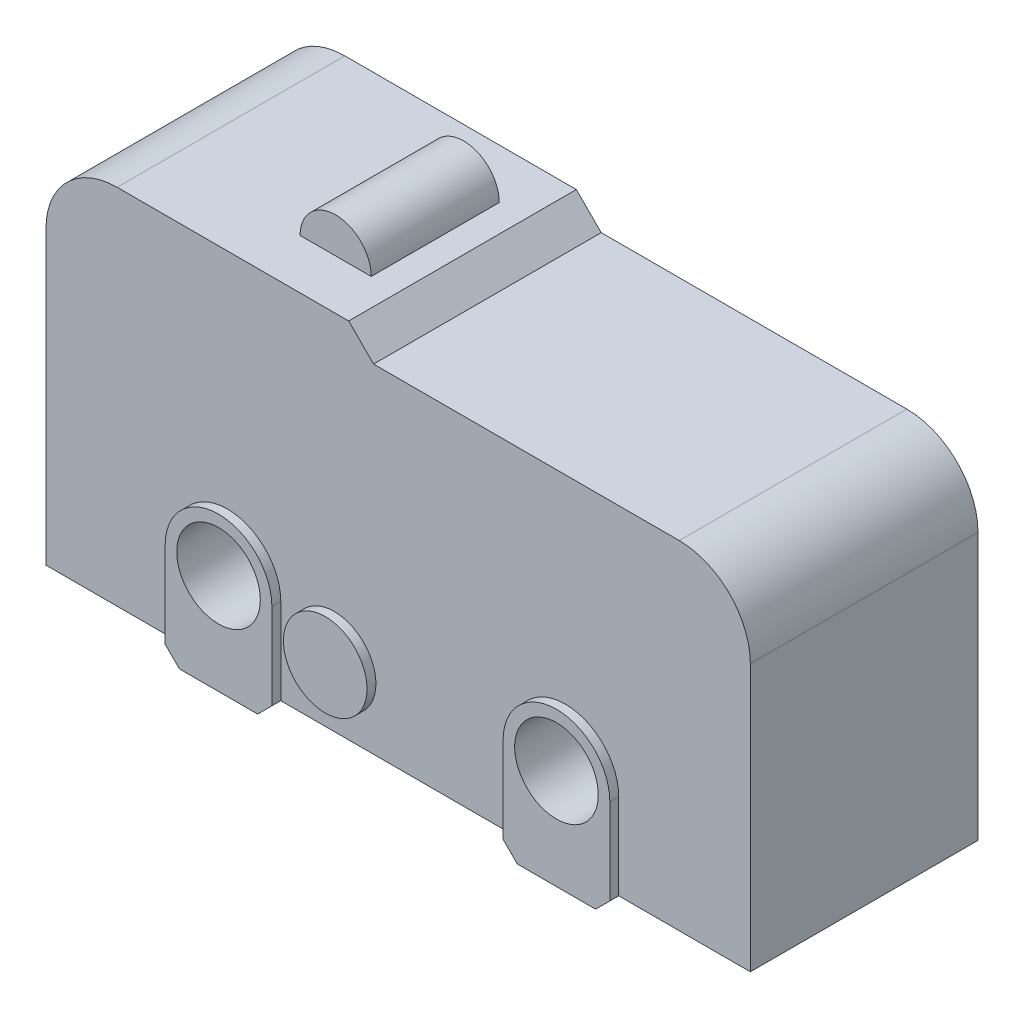
SolidWorks part; units mm, degrees
ref_plane "Front Plane" through (0, 0, 0) normal (0, 0, 1) x (1, 0, 0)
ref_plane "Top Plane" through (0, 0, 0) normal (0, 1, 0) x (1, 0, 0)
ref_plane "Right Plane" through (0, 0, 0) normal (1, 0, 0) x (0, 0, -1)
sketch "Sketch1" plane through (0, 0, 0) normal (0, 0, 1) x (1, 0, 0)
  line L0 (-6.3, 2.5) -> (-6.3, 0.0821)
  line L1 (-9.9, 0.0821) -> (-6.3, 0.0821)
  line L2 (-9.9, 0.0821) -> (-9.9, 8.2821)
  line L3 (-7.9, 10.2821) -> (-2.7324, 10.2821)
  line L4 (9.9, 0.0821) -> (9.9, 7.5821)
  line L5 (-5.9, -0.3179) -> (-6.3, 0.0821)
  line L6 (-3.3, 0.0821) -> (-3.3, 2.5)
  line L7 (-5.9, -0.3179) -> (-3.7, -0.3179)
  line L8 (3.2, 2.5) -> (3.2, 0.0821)
  line L9 (6.2, 2.5) -> (6.2, 0.0821)
  line L10 (-3.7, -0.3179) -> (-3.3, 0.0821)
  line L11 (3.2, 0.0821) -> (3.6, -0.3179)
  line L12 (3.6, -0.3179) -> (5.8, -0.3179)
  line L13 (5.8, -0.3179) -> (6.2, 0.0821)
  line L14 (-3.3, 0.0821) -> (3.2, 0.0821)
  line L15 (6.2, 0.0821) -> (9.9, 0.0821)
  line L16 (7.9, 9.5821) -> (-2.0324, 9.5821)
  line L17 (-2.7324, 10.2821) -> (-2.0324, 9.5821)
  circle A0 centre (-4.8, 2.5) radius 1.175
  circle A1 centre (4.7, 2.5) radius 1.175
  arc A2 (-3.3, 2.5) -> (-6.3, 2.5) centre (-4.8, 2.5) ccw
  arc A3 (6.2, 2.5) -> (3.2, 2.5) centre (4.7, 2.5) ccw
  circle A4 centre (-1.8, 1.8321) radius 1.175
  arc A5 (-9.9, 8.2821) -> (-7.9, 10.2821) centre (-7.9, 8.2821) cw
  arc A6 (7.9, 9.5821) -> (9.9, 7.5821) centre (7.9, 7.5821) cw
  arc A7 (-3.8, 10.2821) -> (-5.8, 10.2821) centre (-4.8, 10.2821) ccw
  point P25 (-9.9, 10.2821)
  dimension "D4" = 2.35
  dimension "D5" = 2.35
  dimension "D6" = 2.35
  dimension "D10" = 3
  dimension "D11" = 3
  dimension "D19" = 2
  dimension "D22" = 2
  dimension "D23" = 2
  dimension "D1" = 19.8
  dimension "D2" = 10.2
  dimension "D3" = 9.9
  dimension "D7" = 1.5
  dimension "D8" = 5.1
  dimension "D9" = 9.5
  dimension "D12" = 1.75
  dimension "D13" = 0.4
  dimension "D14" = 0.4
  dimension "D15" = 45
  dimension "D16" = 45
  dimension "D17" = 45
  dimension "D18" = 45
  dimension "D20" = 9.5
  dimension "D21" = 45
sketch "Sketch2" plane through (0, 0, 0) normal (0, 0, 1) x (1, 0, 0)
  line L0 (-7.9, 10.2821) -> (-2.7324, 10.2821) construction
  line L2 (7.9, 9.5821) -> (-2.0324, 9.5821) construction
  line L3 (9.9, 0.0821) -> (9.9, 7.5821) construction
  line L4 (6.2, 0.0821) -> (9.9, 0.0821) construction
  line L5 (5.8, -0.3179) -> (6.2, 0.0821) construction
  line L6 (3.6, -0.3179) -> (5.8, -0.3179) construction
  line L7 (3.2, 0.0821) -> (3.6, -0.3179) construction
  line L8 (-3.3, 0.0821) -> (3.2, 0.0821) construction
  line L9 (-3.7, -0.3179) -> (-3.3, 0.0821) construction
  line L10 (-5.9, -0.3179) -> (-3.7, -0.3179) construction
  line L11 (-5.9, -0.3179) -> (-6.3, 0.0821) construction
  line L12 (-9.9, 0.0821) -> (-6.3, 0.0821) construction
  line L13 (-9.9, 0.0821) -> (-9.9, 8.2821) construction
  line L14 (-7.9, 10.2821) -> (-1.3912, 10.2821)
  line L15 (-1.3912, 10.2821) -> (-0.6912, 9.5821)
  line L16 (7.9, 9.5821) -> (-0.6912, 9.5821)
  line L17 (9.9, 0.0821) -> (9.9, 7.5821)
  line L18 (6.2, 0.0821) -> (9.9, 0.0821)
  line L19 (5.8, -0.3179) -> (6.2, 0.0821)
  line L20 (3.6, -0.3179) -> (5.8, -0.3179)
  line L21 (3.2, 0.0821) -> (3.6, -0.3179)
  line L22 (-3.3, 0.0821) -> (3.2, 0.0821)
  line L23 (-3.7, -0.3179) -> (-3.3, 0.0821)
  line L24 (-5.9, -0.3179) -> (-3.7, -0.3179)
  line L25 (-5.9, -0.3179) -> (-6.3, 0.0821)
  line L26 (-9.9, 0.0821) -> (-6.3, 0.0821)
  line L27 (-9.9, 0.0821) -> (-9.9, 8.2821)
  arc A0 (-7.9, 10.2821) -> (-9.9, 8.2821) centre (-7.9, 8.2821) ccw construction
  arc A1 (9.9, 7.5821) -> (7.9, 9.5821) centre (7.9, 7.5821) ccw construction
  arc A2 (-7.9, 10.2821) -> (-9.9, 8.2821) centre (-7.9, 8.2821) ccw
  arc A3 (9.9, 7.5821) -> (7.9, 9.5821) centre (7.9, 7.5821) ccw
extrude "Boss-Extrude1" add sketch "Sketch2" along normal blind 6.4
sketch "Sketch4" plane through (0, 0, 6.4) normal (0, 0, 1) x (1, 0, 0)
  line L0 (-6.3, 2.5) -> (-6.3, 0.0821) construction
  line L1 (-3.3, 0.0821) -> (-3.3, 2.5) construction
  line L2 (-3.7, -0.3179) -> (-3.3, 0.0821) construction
  line L3 (-5.9, -0.3179) -> (-3.7, -0.3179) construction
  line L4 (-5.9, -0.3179) -> (-6.3, 0.0821) construction
  line L5 (3.2, 2.5) -> (3.2, 0.0821) construction
  line L6 (6.2, 2.5) -> (6.2, 0.0821) construction
  line L7 (5.8, -0.3179) -> (6.2, 0.0821) construction
  line L8 (3.6, -0.3179) -> (5.8, -0.3179) construction
  line L9 (3.2, 0.0821) -> (3.6, -0.3179) construction
  line L10 (-6.3, 2.5) -> (-6.3, 0.0821)
  line L11 (-3.3, 0.0821) -> (-3.3, 2.5)
  line L12 (-3.7, -0.3179) -> (-3.3, 0.0821)
  line L13 (-5.9, -0.3179) -> (-3.7, -0.3179)
  line L14 (-5.9, -0.3179) -> (-6.3, 0.0821)
  line L15 (3.2, 2.5) -> (3.2, 0.0821)
  line L16 (6.2, 2.5) -> (6.2, 0.0821)
  line L17 (5.8, -0.3179) -> (6.2, 0.0821)
  line L18 (3.6, -0.3179) -> (5.8, -0.3179)
  line L19 (3.2, 0.0821) -> (3.6, -0.3179)
  arc A0 (-3.3, 2.5) -> (-6.3, 2.5) centre (-4.8, 2.5) ccw construction
  arc A1 (6.2, 2.5) -> (3.2, 2.5) centre (4.7, 2.5) ccw construction
  circle A2 centre (-1.8, 1.8321) radius 1.175 construction
  arc A3 (-3.3, 2.5) -> (-6.3, 2.5) centre (-4.8, 2.5) ccw
  arc A4 (6.2, 2.5) -> (3.2, 2.5) centre (4.7, 2.5) ccw
  circle A5 centre (-1.8, 1.8321) radius 1.175
extrude "Boss-Extrude2" add sketch "Sketch4" along normal blind 0.25
sketch "Sketch5" plane through (0, 0, 0) normal (0, 0, -1) x (-1, 0, 0)
  line L0 (6.3, 2.5) -> (6.3, 0.0821) construction
  line L1 (6.3, 0.0821) -> (5.9, -0.3179) construction
  line L2 (5.9, -0.3179) -> (3.7, -0.3179) construction
  line L3 (3.7, -0.3179) -> (3.3, 0.0821) construction
  line L4 (3.3, 0.0821) -> (3.3, 2.5) construction
  line L5 (-3.2, 2.5) -> (-3.2, 0.0821) construction
  line L6 (-3.2, 0.0821) -> (-3.6, -0.3179) construction
  line L7 (-3.6, -0.3179) -> (-5.8, -0.3179) construction
  line L8 (-5.8, -0.3179) -> (-6.2, 0.0821) construction
  line L9 (-6.2, 0.0821) -> (-6.2, 2.5) construction
  line L10 (6.3, 2.5) -> (6.3, 0.0821)
  line L11 (6.3, 0.0821) -> (5.9, -0.3179)
  line L12 (5.9, -0.3179) -> (3.7, -0.3179)
  line L13 (3.7, -0.3179) -> (3.3, 0.0821)
  line L14 (3.3, 0.0821) -> (3.3, 2.5)
  line L15 (-3.2, 2.5) -> (-3.2, 0.0821)
  line L16 (-3.2, 0.0821) -> (-3.6, -0.3179)
  line L17 (-3.6, -0.3179) -> (-5.8, -0.3179)
  line L18 (-5.8, -0.3179) -> (-6.2, 0.0821)
  line L19 (-6.2, 0.0821) -> (-6.2, 2.5)
  arc A0 (6.3, 2.5) -> (3.3, 2.5) centre (4.8, 2.5) ccw construction
  circle A1 centre (1.8, 1.8321) radius 1.175 construction
  arc A2 (-3.2, 2.5) -> (-6.2, 2.5) centre (-4.7, 2.5) ccw construction
  arc A3 (6.3, 2.5) -> (3.3, 2.5) centre (4.8, 2.5) ccw
  circle A4 centre (1.8, 1.8321) radius 1.175
  arc A5 (-3.2, 2.5) -> (-6.2, 2.5) centre (-4.7, 2.5) ccw
extrude "Boss-Extrude3" add sketch "Sketch5" along normal blind 0.25
sketch "Sketch6" plane through (0, 0, 6.65) normal (0, 0, 1) x (1, 0, 0)
  circle A0 centre (-4.8, 2.5) radius 1.175 construction
  circle A1 centre (4.7, 2.5) radius 1.175 construction
  circle A2 centre (-4.8, 2.5) radius 1.175
  circle A3 centre (4.7, 2.5) radius 1.175
extrude "Cut-Extrude1" cut sketch "Sketch6" against normal through all
ref_plane "Plane1" through (0, 0, 3.2) normal (0, 0, 1) x (1, 0, 0)
sketch "Sketch7" plane through (0, 0, 3.2) normal (0, 0, 1) x (1, 0, 0)
  line L0 (-7.9, 10.2821) -> (-2.7324, 10.2821) construction
  line L1 (-4.158, 10.2821) -> (-2.158, 10.2821)
  line L3 (-1.3912, 10.2821) -> (-7.9, 10.2821) construction
  arc A2 (-2.158, 10.2821) -> (-4.158, 10.2821) centre (-3.158, 10.2821) ccw
  dimension "D1" = 2
extrude "Boss-Extrude4" add sketch "Sketch7" along normal blind 1.8 and the other way blind 1.8
